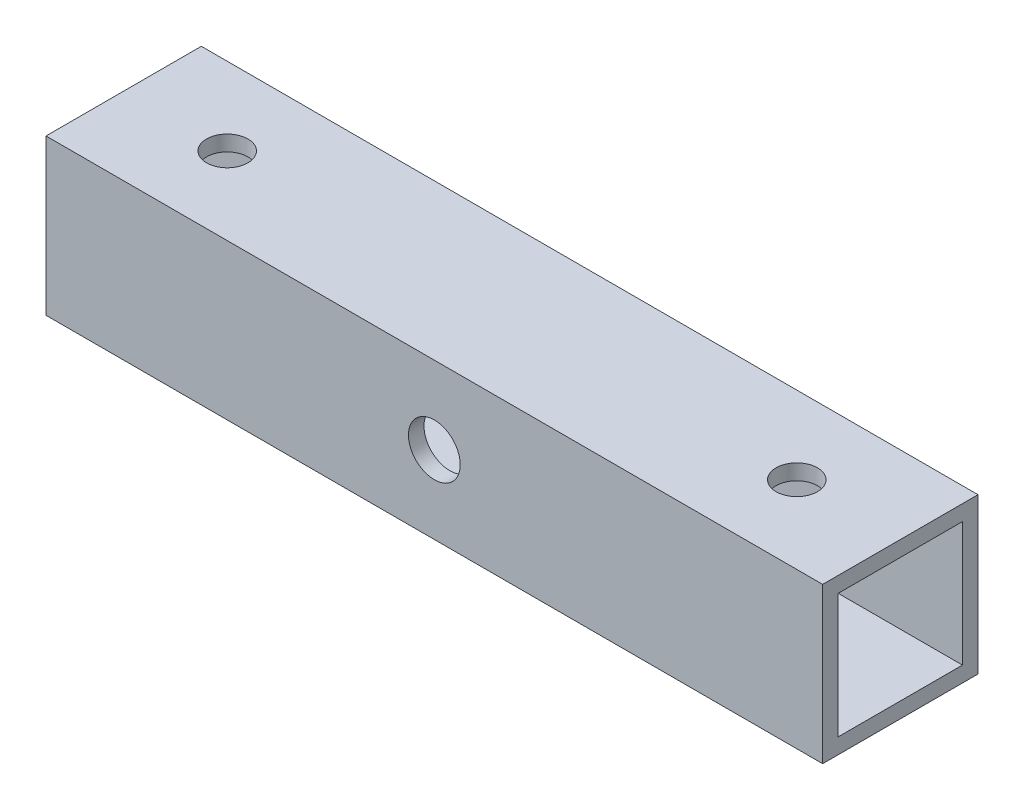
SolidWorks part; units mm, degrees
ref_plane "Front Plane" through (0, 0, 0) normal (0, 0, 1) x (1, 0, 0)
ref_plane "Top Plane" through (0, 0, 0) normal (0, 1, 0) x (1, 0, 0)
ref_plane "Right Plane" through (0, 0, 0) normal (1, 0, 0) x (0, 0, -1)
sketch "Sketch1" plane through (0, 0, 0) normal (0, 0, 1) x (1, 0, 0)
  line L1 (-75, 15) -> (75, 15)
  line L2 (-75, 15) -> (-75, -15)
  line L3 (-75, -15) -> (75, -15)
  line L4 (75, 15) -> (75, -15)
  line L5 (-75, 15) -> (75, -15) construction
  line L6 (-75, -15) -> (75, 15) construction
  point P0 (0, 0)
  dimension "D1" = 150
  dimension "D2" = 30
extrude "Boss-Extrude1" add sketch "Sketch1" along normal blind 30
shell "Shell1" thickness 3
sketch "Sketch2" plane through (0, 0, 30) normal (0, 0, 1) x (1, 0, 0)
  circle A0 centre (0, 0) radius 5
  dimension "D1" = 10
extrude "Cut-Extrude1" cut sketch "Sketch2" against normal blind 30
sketch "Sketch3" plane through (0, 15, 0) normal (0, 1, 0) x (1, 0, 0)
  line L0 (-75, -30) -> (-75, 0) construction
  line L1 (75, -30) -> (75, 0) construction
  circle A0 centre (-55, -15) radius 4
  circle A1 centre (55, -15) radius 4
  dimension "D1" = 8
  dimension "D3" = 8
  dimension "D2" = 20
  dimension "D4" = 20
extrude "Cut-Extrude2" cut sketch "Sketch3" against normal blind 36
